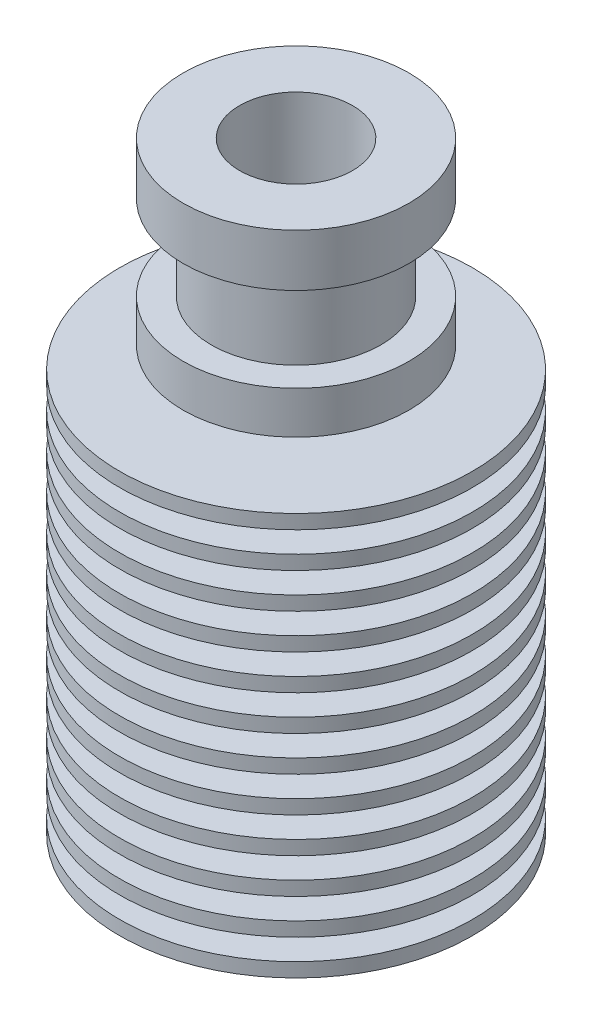
SolidWorks part; units mm, degrees
material "1060 Alloy"
ref_plane "Front Plane" through (0, 0, 0) normal (0, 0, 1) x (1, 0, 0)
ref_plane "Top Plane" through (0, 0, 0) normal (0, 1, 0) x (1, 0, 0)
ref_plane "Right Plane" through (0, 0, 0) normal (1, 0, 0) x (0, 0, -1)
sketch "Sketch1" plane through (0, 0, 0) normal (0, 0, 1) x (1, 0, 0)
  line L0 (0, -21.35) -> (0, 21.35) construction
  line L1 (3.5, -21.35) -> (12.5, -21.35)
  line L2 (12.5, -21.35) -> (12.5, -20.35)
  line L3 (12.5, -20.35) -> (6.24, -20.35)
  line L4 (6.24, -20.35) -> (6.24, -18.85)
  line L5 (6.24, -18.85) -> (12.5, -18.85)
  line L6 (12.5, -18.85) -> (12.5, -17.85)
  line L7 (12.5, -17.85) -> (6.0558, -17.85)
  line L8 (6.0558, -17.85) -> (6.0558, -16.35)
  line L9 (6.0558, -16.35) -> (12.5, -16.35)
  line L10 (12.5, -16.35) -> (12.5, -15.35)
  line L11 (4.3975, 8.65) -> (4.3975, 7.15)
  line L12 (4.3975, 7.15) -> (12.5, 7.15)
  line L13 (12.5, 7.15) -> (12.5, 6.15)
  line L14 (12.5, 6.15) -> (4.3975, 6.15)
  line L15 (4.3975, 6.15) -> (4.3975, 4.65)
  line L16 (4.3975, 4.65) -> (12.5, 4.65)
  line L17 (12.5, 4.65) -> (12.5, 3.65)
  line L18 (12.5, 3.65) -> (4.5818, 3.65)
  line L19 (4.5818, 3.65) -> (4.5818, 2.15)
  line L20 (4.5818, 2.15) -> (12.5, 2.15)
  line L21 (12.5, 2.15) -> (12.5, 1.15)
  line L22 (12.5, 1.15) -> (4.766, 1.15)
  line L23 (4.766, 1.15) -> (4.766, -0.35)
  line L24 (4.766, -0.35) -> (12.5, -0.35)
  line L25 (12.5, -0.35) -> (12.5, -1.35)
  line L26 (12.5, -1.35) -> (4.9503, -1.35)
  line L27 (4.9503, -1.35) -> (4.9503, -2.85)
  line L28 (4.9503, -2.85) -> (12.5, -2.85)
  line L29 (12.5, -2.85) -> (12.5, -3.85)
  line L30 (12.5, -3.85) -> (5.1345, -3.85)
  line L31 (5.1345, -3.85) -> (5.1345, -5.35)
  line L32 (5.1345, -5.35) -> (12.5, -5.35)
  line L33 (12.5, -5.35) -> (12.5, -6.35)
  line L34 (12.5, -6.35) -> (5.3188, -6.35)
  line L35 (5.3188, -6.35) -> (5.3188, -7.85)
  line L36 (5.3188, -7.85) -> (12.5, -7.85)
  line L37 (12.5, -7.85) -> (12.5, -8.85)
  line L38 (12.5, -8.85) -> (5.503, -8.85)
  line L39 (5.503, -8.85) -> (5.503, -10.35)
  line L40 (5.503, -10.35) -> (12.5, -10.35)
  line L41 (12.5, -10.35) -> (12.5, -11.35)
  line L42 (12.5, -11.35) -> (5.6873, -11.35)
  line L43 (5.6873, -11.35) -> (5.6873, -12.85)
  line L44 (5.6873, -12.85) -> (12.5, -12.85)
  line L45 (4.3975, 8.65) -> (8, 8.65)
  line L46 (8, 8.65) -> (8, 11.65)
  line L47 (8, 11.65) -> (6, 11.65)
  line L48 (6, 11.65) -> (6, 17.65)
  line L49 (6, 17.65) -> (8, 17.65)
  line L50 (8, 17.65) -> (8, 21.35)
  line L51 (3.5, -21.35) -> (3.5, -6.55)
  line L52 (3.5, -6.55) -> (2.1, -5.7417)
  line L55 (2.1, -5.7417) -> (2.1, 10.253)
  line L56 (2.1, 10.253) -> (4, 11.35)
  line L57 (4, 11.35) -> (4, 21.35)
  line L58 (4, 21.35) -> (8, 21.35)
  line L59 (12.5, -12.85) -> (12.5, -13.85)
  line L60 (12.5, -13.85) -> (5.8715, -13.85)
  line L61 (5.8715, -13.85) -> (5.8715, -15.35)
  line L62 (5.8715, -15.35) -> (12.5, -15.35)
  line L63 (6.24, -18.85) -> (4.3975, 6.15) construction
  dimension "D2" = 3.5
  dimension "D3" = 25
  dimension "D4" = 1
  dimension "D5" = 1.5
  dimension "D6" = 42.7
  dimension "D7" = 12.48
  dimension "D8" = 8.795
  dimension "D9" = 9.7
  dimension "D10" = 3.7
  dimension "D11" = 16
  dimension "D12" = 12.7
  dimension "D14" = 12
  dimension "D16" = 4.2
  dimension "D17" = 14.8
  dimension "D19" = 10
  dimension "D20" = 120
  dimension "D21" = 4
  dimension "D23" = 120
revolve "Revolve1" add sketch "Sketch1" angle 360 about L0
